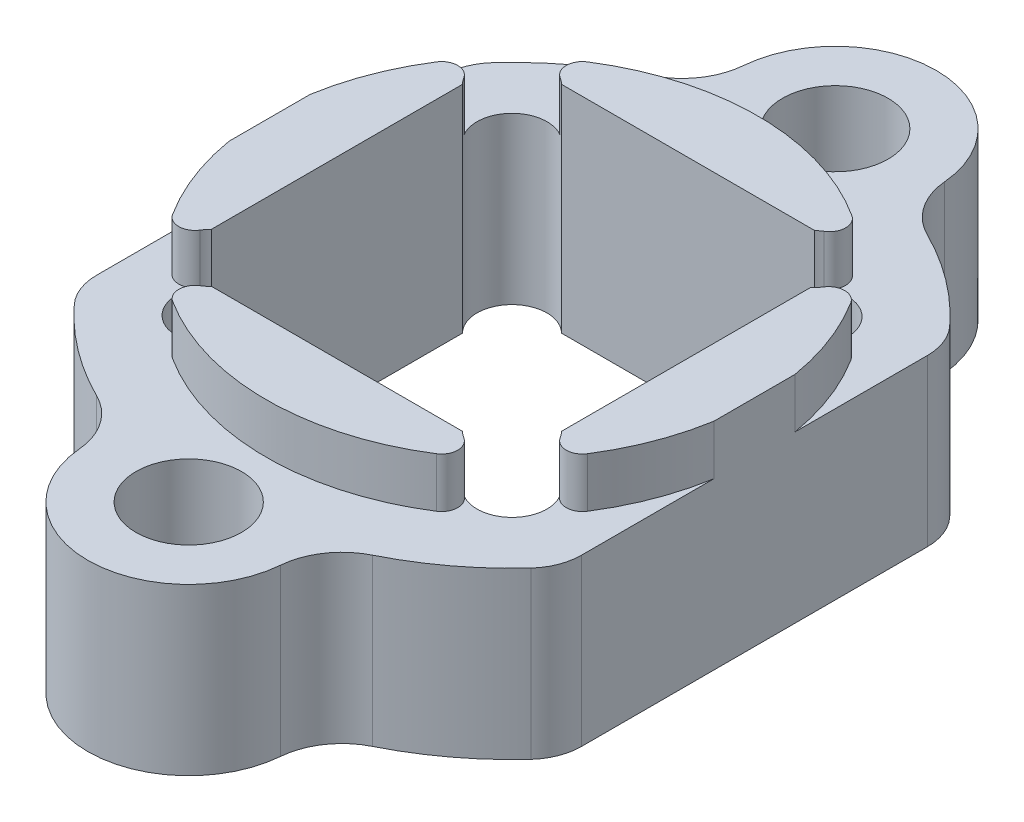
SolidWorks part; units mm, degrees
material "Alum Plate"
ref_plane "Front Plane" through (0, 0, 0) normal (0, 0, 1) x (1, 0, 0)
ref_plane "Top Plane" through (0, 0, 0) normal (0, 1, 0) x (1, 0, 0)
ref_plane "Right Plane" through (0, 0, 0) normal (1, 0, 0) x (0, 0, -1)
other "Bounding Box"
ref_plane "Default Plane" through (-8.9266, -12.7485, 0) normal (-0.1736, 0.9848, 0) x (0.9848, 0.1736, 0)
sketch "Sketch1" plane through (0, 0, 0) normal (0, 1, 0) x (1, 0, 0)
  line L0 (0, 0) -> (0, 15.24) construction
  line L1 (-8.2499, 8.2499) -> (8.2499, 8.2499)
  line L2 (-8.2499, 8.2499) -> (-8.2499, -8.2499)
  line L3 (-8.2499, -8.2499) -> (8.2499, -8.2499)
  line L4 (8.2499, 8.2499) -> (8.2499, -8.2499)
  line L5 (-8.2499, 8.2499) -> (8.2499, -8.2499) construction
  line L6 (-8.2499, -8.2499) -> (8.2499, 8.2499) construction
  line L7 (0, 0) -> (0, -15.24) construction
  circle A0 centre (0, 15.24) radius 2.4892
  circle A1 centre (0, -15.24) radius 2.4892
  arc A2 (-4.5624, 13.8741) -> (4.5624, 13.8741) centre (0, 15.24) cw
  arc A3 (4.5624, -13.8741) -> (-4.5624, -13.8741) centre (0, -15.24) cw
  arc A4 (4.5624, 13.8741) -> (4.5624, -13.8741) centre (0, 0) cw
  arc A5 (-4.5624, -13.8741) -> (-4.5624, 13.8741) centre (0, 0) cw
  circle A6 centre (0, 0) radius 10.9753 construction
  point P0 (0, 0)
  dimension "D2" = 4.9784
  dimension "D3" = 4.7625
  dimension "D5" = 21.9507
  dimension "D6" = 14.605
  dimension "D1" = 16.4998
  dimension "D4" = 15.24
extrude "Boss-Extrude1" add sketch "Sketch1" along normal mid plane 10.16
sketch "Sketch2" plane through (0, 5.08, 0) normal (0, 1, 0) x (1, 0, 0)
  line L0 (-11.43, -9.0918) -> (-11.43, 9.0918)
  line L1 (11.43, -9.0918) -> (11.43, 9.0918)
  arc A0 (-4.5624, 13.8741) -> (-4.5624, -13.8741) centre (0, 0) ccw construction
  arc A1 (4.5624, -13.8741) -> (4.5624, 13.8741) centre (0, 0) ccw construction
  arc A2 (-11.43, -9.0918) -> (-11.43, 9.0918) centre (0, 0) cw
  arc A3 (11.43, 9.0918) -> (11.43, -9.0918) centre (0, 0) cw
  point P11 (11.7206, -9.0535)
  point P14 (0.3639, 0)
  dimension "D1" = 22.86
extrude "Cut-Extrude1" cut sketch "Sketch2" against normal through all
sketch "Sketch4" plane through (0, 5.08, 0) normal (0, 1, 0) x (1, 0, 0)
  line L0 (-8.2499, -8.2499) -> (8.2499, 8.2499) construction
  circle A0 centre (0, 0) radius 11.5887
  circle A2 centre (0, 0) radius 20.0025
  arc A3 (-4.5624, -13.8741) -> (4.5624, -13.8741) centre (0, -15.24) ccw construction
  dimension "D1" = 23.1775
extrude "Cut-Extrude2" cut sketch "Sketch4" against normal blind 2.3495
sketch "Sketch6" plane through (0, 5.08, 0) normal (0, 1, 0) x (1, 0, 0)
  line L0 (-8.2499, -8.2499) -> (8.2499, 8.1387) construction
  line L1 (8.2499, -8.2499) -> (-8.2499, 8.2499) construction
  circle A0 centre (-7.0825, 7.0825) radius 1.651
  circle A1 centre (7.1355, 7.0318) radius 1.651
  circle A2 centre (7.0825, -7.0825) radius 1.651
  circle A3 centre (-7.0785, -7.0864) radius 1.651
  point P18 (0, 0)
  point P19 (0, 0)
  point P20 (0, 0)
  point P21 (0, 0)
  point P22 (8.2499, -8.2499)
  dimension "D1" = 3.302
extrude "Cut-Extrude3" cut sketch "Sketch6" against normal through all
fillet "Fillet1" radius 0.762 8 edges at (-7.8033, 3.9053, -8.5678) (-8.5678, 3.9053, -7.8033) (8.6289, 3.9053, -7.7357) (7.8612, 3.9053, -8.5147) (7.8033, 3.9053, 8.5678) (8.5678, 3.9053, 7.8033) (-8.5635, 3.9053, 7.8081) (-7.7985, 3.9053, 8.5722)
fillet "Fillet2" radius 3.175 4 edges at (-4.5624, -1.1747, -13.8741) (4.5624, -1.1747, -13.8741) (4.5624, -1.1747, 13.8741) (-4.5624, -1.1747, 13.8741)
fillet "Fillet3" radius 2.54 4 edges at (-11.43, -1.1747, -9.0918) (-11.43, -1.1747, 9.0918) (11.43, -1.1747, 9.0918) (11.43, -1.1747, -9.0918)
